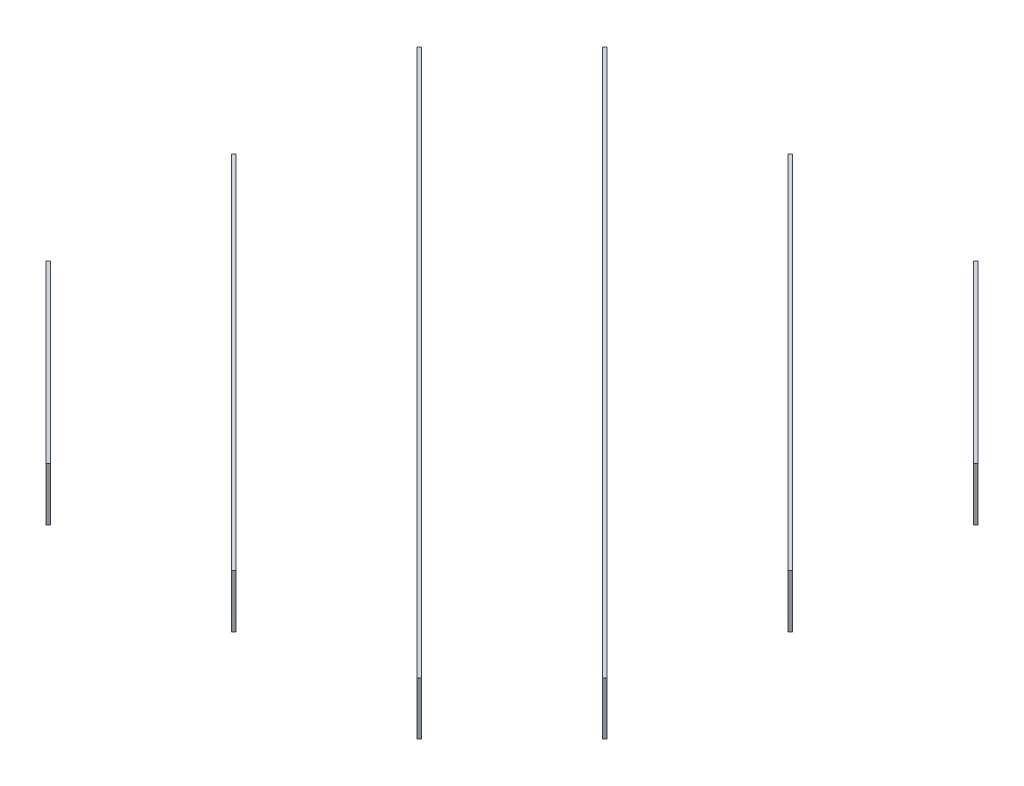
SolidWorks part; units mm, degrees
material "Plain Carbon Steel"
ref_plane "Front" through (0, 0, 0) normal (0, 0, 1) x (1, 0, 0)
ref_plane "Top" through (0, 0, 0) normal (0, 1, 0) x (1, 0, 0)
ref_plane "Right" through (0, 0, 0) normal (1, 0, 0) x (0, 0, -1)
sketch "Sketch1" plane through (0, 0, 0) normal (0, 1, 0) x (1, 0, 0)
  line L0 (-525, -525) -> (-525, 525) construction
  line L1 (-605, 605) -> (605, 605) construction
  line L2 (-605, 605) -> (-605, -605) construction
  line L3 (-605, -605) -> (605, -605) construction
  line L4 (605, 605) -> (605, -605) construction
  line L5 (-605, 605) -> (605, -605) construction
  line L6 (-605, -605) -> (605, 605) construction
  line L7 (-525, 525) -> (525, 525) construction
  line L8 (-525, 350) -> (525, 350) construction
  line L9 (-525, 175) -> (525, 175) construction
  line L10 (-525, 0) -> (525, 0) construction
  line L11 (-525, -175) -> (525, -175) construction
  line L12 (-525, -350) -> (525, -350) construction
  line L13 (-525, -525) -> (525, -525) construction
  line L14 (-350, -525) -> (-350, 525) construction
  line L15 (-175, -525) -> (-175, 525) construction
  line L16 (0, -525) -> (0, 525) construction
  line L17 (175, -525) -> (175, 525) construction
  line L18 (350, -525) -> (350, 525) construction
  line L19 (525, -525) -> (525, 525) construction
  line L20 (525, -525) -> (0, -1050) construction
  line L21 (0, -1050) -> (-525, -525) construction
  line L22 (0, -1050) -> (0, 0) construction
  point P0 (0, 0)
  dimension "D1" = 1210
  dimension "D2" = 1210
  dimension "D5" = 175
  dimension "D3" = 7
  dimension "D4" = 7
sketch "Sketch2" plane through (0, 0, 0) normal (0, 1, 0) x (1, 0, 0)
  line L0 (-605, -274.2426) -> (-274.2426, -605)
  line L1 (-602.8787, 602.8787) -> (602.8787, 602.8787) construction
  line L2 (-602.8787, 602.8787) -> (-602.8787, -602.8787) construction
  line L3 (-602.8787, -602.8787) -> (602.8787, -602.8787) construction
  line L4 (602.8787, 602.8787) -> (602.8787, -602.8787) construction
  line L5 (-602.8787, 602.8787) -> (602.8787, -602.8787) construction
  line L6 (-602.8787, -602.8787) -> (602.8787, 602.8787) construction
  line L7 (-605, 605) -> (605, -605) construction
  line L8 (-427.8787, 602.8787) -> (602.8787, -427.8787) construction
  line L9 (-77.8787, 602.8787) -> (602.8787, -77.8787) construction
  line L10 (272.1213, 602.8787) -> (602.8787, 272.1213) construction
  line L11 (-602.8787, -272.1213) -> (-272.1213, -602.8787) construction
  line L12 (-602.8787, 77.8787) -> (77.8787, -602.8787) construction
  line L13 (-602.8787, 427.8787) -> (427.8787, -602.8787) construction
  line L14 (-605, 75.7574) -> (75.7574, -605)
  line L15 (-605, 425.7574) -> (425.7574, -605)
  line L16 (-430, 600.7574) -> (600.7574, -430)
  line L17 (-80, 600.7574) -> (600.7574, -80)
  line L18 (270, 600.7574) -> (600.7574, 270)
  line L19 (-600.7574, -270) -> (-270, -600.7574)
  line L20 (-600.7574, 80) -> (80, -600.7574)
  line L21 (-600.7574, 430) -> (430, -600.7574)
  line L22 (-425.7574, 605) -> (605, -425.7574)
  line L23 (-75.7574, 605) -> (605, -75.7574)
  line L24 (274.2426, 605) -> (605, 274.2426)
  line L25 (-605, -274.2426) -> (-600.7574, -270)
  line L26 (-274.2426, -605) -> (-270, -600.7574)
  line L27 (-605, 75.7574) -> (-600.7574, 80)
  line L28 (75.7574, -605) -> (80, -600.7574)
  line L29 (-605, 425.7574) -> (-600.7574, 430)
  line L30 (425.7574, -605) -> (430, -600.7574)
  line L31 (-430, 600.7574) -> (-425.7574, 605)
  line L32 (600.7574, -430) -> (605, -425.7574)
  line L33 (-80, 600.7574) -> (-75.7574, 605)
  line L34 (600.7574, -80) -> (605, -75.7574)
  line L35 (270, 600.7574) -> (274.2426, 605)
  line L36 (600.7574, 270) -> (605, 274.2426)
  line L38 (-605, 605) -> (605, 605) construction
  line L39 (605, 605) -> (605, -605) construction
extrude "Boss-Extrude1" add sketch "Sketch2" along normal blind 100
sketch "Sketch3" plane through (-439.6213, 0, 439.6213) normal (-0.7071, 0, 0.7071) x (0.7071, 0, 0.7071)
  line L0 (-742.4621, 0) -> (0, 0) construction
  line L1 (-126.7056, 50) -> (-120.7056, 50)
  line L2 (-126.7056, 50) -> (-126.7056, -50)
  line L3 (-126.7056, -50) -> (-120.7056, -50)
  line L4 (-120.7056, 50) -> (-120.7056, -50)
  line L5 (-126.7056, 50) -> (-120.7056, -50) construction
  line L6 (-126.7056, -50) -> (-120.7056, 50) construction
  line L7 (123.7437, 0) -> (-618.7184, 0) construction
  line L8 (-374.2311, 50) -> (-368.2311, 50)
  line L9 (-374.2311, 50) -> (-374.2311, -50)
  line L10 (-374.2311, -50) -> (-368.2311, -50)
  line L11 (-368.2311, 50) -> (-368.2311, -50)
  line L12 (-374.2311, 50) -> (-368.2311, -50) construction
  line L13 (-374.2311, -50) -> (-368.2311, 50) construction
  line L14 (-621.7184, 50) -> (-615.7184, 50)
  line L15 (-621.7184, 50) -> (-621.7184, -50)
  line L16 (-621.7184, -50) -> (-615.7184, -50)
  line L17 (-615.7184, 50) -> (-615.7184, -50)
  line L18 (-621.7184, 50) -> (-615.7184, -50) construction
  line L19 (-621.7184, -50) -> (-615.7184, 50) construction
  line L20 (0, 0) -> (0, 100) construction
  line L21 (-233.8808, 100) -> (233.8808, 100) construction
  line L22 (621.7184, -50) -> (615.7184, 50) construction
  line L23 (621.7184, 50) -> (615.7184, -50) construction
  line L24 (374.2311, -50) -> (368.2311, 50) construction
  line L25 (374.2311, 50) -> (368.2311, -50) construction
  line L26 (126.7056, -50) -> (120.7056, 50) construction
  line L27 (126.7056, 50) -> (120.7056, -50) construction
  line L28 (615.7184, 50) -> (615.7184, -50)
  line L29 (621.7184, -50) -> (615.7184, -50)
  line L30 (621.7184, 50) -> (621.7184, -50)
  line L31 (621.7184, 50) -> (615.7184, 50)
  line L32 (368.2311, 50) -> (368.2311, -50)
  line L33 (374.2311, -50) -> (368.2311, -50)
  line L34 (374.2311, 50) -> (374.2311, -50)
  line L35 (374.2311, 50) -> (368.2311, 50)
  line L36 (120.7056, 50) -> (120.7056, -50)
  line L37 (126.7056, -50) -> (120.7056, -50)
  line L38 (126.7056, 50) -> (126.7056, -50)
  line L39 (126.7056, 50) -> (120.7056, 50)
  circle A0 centre (-126.7056, 50) radius 1.5
  circle A1 centre (-120.7056, 50) radius 1.5
  circle A2 centre (-621.7184, 50) radius 1.5
  circle A3 centre (-615.7184, 50) radius 1.5
  circle A4 centre (-374.2311, 50) radius 1.5
  circle A5 centre (-368.2311, 50) radius 1.5
  circle A6 centre (368.2311, 50) radius 1.5
  circle A7 centre (374.2311, 50) radius 1.5
  circle A8 centre (615.7184, 50) radius 1.5
  circle A9 centre (621.7184, 50) radius 1.5
  circle A10 centre (120.7056, 50) radius 1.5
  circle A11 centre (126.7056, 50) radius 1.5
  point P0 (-123.7056, 0)
  point P7 (-371.2311, 0)
  point P12 (-618.7184, 0)
  point P48 (618.7184, 0)
  point P49 (371.2311, 0)
  point P50 (123.7056, 0)
  line M15 (-233.8808, 0) -> (233.8808, 0)
  dimension "D1" = 100
  dimension "D7" = 3
  dimension "D8" = 3
  dimension "D9" = 3
  dimension "D10" = 3
  dimension "D11" = 3
  dimension "D12" = 3
  dimension "D2" = 100
  dimension "D3" = 100
  dimension "D4" = 3
  dimension "D5" = 3
  dimension "D6" = 3
extrude "Cut-Extrude1" cut sketch "Sketch3" against normal through all contours A3 L14 A2 L15 L16 L17 | L14 A2 L15 | L17 A3 L14 | L14 A3 L17 | L15 A2 L14 | L8 A4 L9 | L9 A4 L8 | A5 L8 A4 L9 L10 L11 | L8 A5 L11 | L11 A5 L8 | L1 A0 L2 | L4 A1 L1 | L1 A1 L4 | A1 L1 A0 L2 L4 M15 | L2 A0 L1 | A10 L36 L39 | A10 L39 L36 | L38 A11 L39 A10 L36 M15 | A11 L38 L39 | A11 L39 L38 | A6 L32 L35 | L34 A7 L35 A6 L32 L33 | A7 L35 L34 | A7 L34 L35 | A6 L35 L32 | A8 L28 L31 | A9 L31 L30 | L30 A9 L31 A8 L28 L29 | A9 L30 L31 | A8 L31 L28
sketch "Sketch6" plane through (260.3787, 0, -260.3787) normal (-0.7071, 0, 0.7071) x (0.7071, 0, 0.7071)
  line L0 (-0.0191, 81) -> (-0.0191, 75) construction
  line L1 (14.9809, 81) -> (-15.0191, 81) construction
  line L2 (-15.0191, 75) -> (14.9809, 75) construction
  line L4 (-28.0191, 84) -> (27.9809, 84) construction
  line L5 (-28.0191, 84) -> (-28.0191, 72) construction
  line L6 (-28.0191, 72) -> (27.9809, 72) construction
  line L7 (27.9809, 84) -> (27.9809, 72) construction
  line L8 (-28.0191, 84) -> (27.9809, 72) construction
  line L9 (-28.0191, 72) -> (27.9809, 84) construction
  line L11 (27.9809, 72) -> (-28.0191, 72)
  line L12 (27.9809, 72) -> (27.9809, 84)
  line L13 (27.9809, 84) -> (-28.0191, 84)
  line L14 (-28.0191, 72) -> (-28.0191, 84)
  point P6 (-0.0191, 78)
  dimension "D1" = 3
extrude "Cut-Extrude3" cut sketch "Sketch6" against normal blind 6
sketch "Sketch7" plane through (-264.6213, 0, 264.6213) normal (-0.7071, 0, 0.7071) x (0.7071, 0, 0.7071)
  line L4 (-28.0191, 72) -> (27.9809, 72)
  line L5 (-28.0191, 72) -> (27.9809, 72)
  line L6 (-28.0191, 84) -> (-28.0191, 72)
  line L7 (-28.0191, 84) -> (-28.0191, 72)
  line L12 (27.9809, 84) -> (-28.0191, 84)
  line L13 (27.9809, 84) -> (-28.0191, 84)
  line L14 (27.9809, 72) -> (27.9809, 84)
  line L15 (27.9809, 72) -> (27.9809, 84)
  dimension "D1" = 0
extrude "Cut-Extrude4" cut sketch "Sketch7" against normal up to next (6 mm away)
sketch "Sketch8" plane through (-439.6213, 0, 439.6213) normal (-0.7071, 0, 0.7071) x (0.7071, 0, 0.7071)
  line L0 (-120.7056, 0) -> (120.7056, 0) construction
  circle A0 centre (0, 0) radius 1.5
  dimension "D1" = 3
extrude "Cut-Extrude5" cut sketch "Sketch8" against normal through all
sketch "Sketch9" plane through (-89.6213, 0, 89.6213) normal (-0.7071, 0, 0.7071) x (0.7071, 0, 0.7071)
  circle A0 centre (0, 16) radius 4
  circle A1 centre (0, 36) radius 4
  dimension "D1" = 8
extrude "Cut-Extrude6" cut sketch "Sketch9" against normal up to surface (253.4874 mm away)
ref_point "Point1"
sketch "Sketch10" plane through (439.6213, 0, -439.6213) normal (0.7071, 0, -0.7071) x (-0.7071, 0, -0.7071)
  line L0 (1.5, 0) -> (-1.5, 0) construction
  line L1 (0, 0) -> (0, 100) construction
  line L2 (-233.8808, 100) -> (233.8808, 100) construction
  circle A0 centre (0, 50) radius 3
  dimension "D1" = 6
extrude "Cut-Extrude7" cut sketch "Sketch10" against normal up to surface (253.4874 mm away)
sketch "Sketch11" plane through (-439.6213, 0, 439.6213) normal (-0.7071, 0, 0.7071) x (0.7071, 0, 0.7071)
  circle A1 centre (0, 50) radius 3
  circle A2 centre (0, 50) radius 3
  dimension "D1" = 0
extrude "Cut-Extrude8" cut sketch "Sketch11" against normal up to surface (253.4874 mm away)
sketch "Sketch12" plane through (264.6213, 0, -264.6213) normal (0.7071, 0, -0.7071) x (-0.7071, 0, -0.7071)
  line L0 (368.2311, 0) -> (126.7056, 0) construction
  line L1 (126.7056, 0) -> (247.4683, 0) construction
  line L2 (247.4683, 0) -> (247.4683, 100) construction
  line L3 (-481.3681, 100) -> (481.3681, 100) construction
  circle A0 centre (247.4683, 50) radius 3
  dimension "D1" = 6
extrude "Cut-Extrude9" cut sketch "Sketch12" against normal up to surface (748.4621 mm away) up to face at (-266.7426, 50, 262.5)
sketch "Sketch13" plane through (89.6213, 0, -89.6213) normal (0.7071, 0, -0.7071) x (-0.7071, 0, -0.7071)
  line L0 (615.7184, 0) -> (374.2311, 0) construction
  line L1 (374.2311, 0) -> (494.9747, 0) construction
  line L2 (494.9747, 0) -> (494.9747, 100) construction
  line L3 (-728.8555, 100) -> (728.8555, 100) construction
  circle A0 centre (494.9747, 50) radius 3
  dimension "D1" = 6
extrude "Cut-Extrude10" cut sketch "Sketch13" against normal up to surface (253.4874 mm away)
ref_plane "Plane1" through (0, 0, 0) normal (0.7071, 0, 0.7071) x (0.7071, 0, -0.7071)
mirror "Mirror1" about plane through (0, 0, 0) normal (0.7071, 0, 0.7071) of "Cut-Extrude9", "Cut-Extrude10"
equation "\"Plate width\"= 100mm"
equation "\"D1@Boss-Extrude1\"=\"Plate width\""
equation "\"D1@Sketch3\"=\"Plate width\""
equation "\"D2@Sketch3\"=\"Plate width\""
equation "\"D3@Sketch3\"=\"Plate width\""
equation "\"D4@Sketch3\"=\"half plate thickness\""
equation "\"D5@Sketch3\"=\"half plate thickness\""
equation "\"D6@Sketch3\"=\"half plate thickness\""
equation "\"D7@Sketch3\"=\"half plate thickness\""
equation "\"D8@Sketch3\"=\"half plate thickness\""
equation "\"D9@Sketch3\"=\"half plate thickness\""
equation "\"D10@Sketch3\"=\"half plate thickness\""
equation "\"D11@Sketch3\"=\"half plate thickness\""
equation "\"D12@Sketch3\"=\"half plate thickness\""
